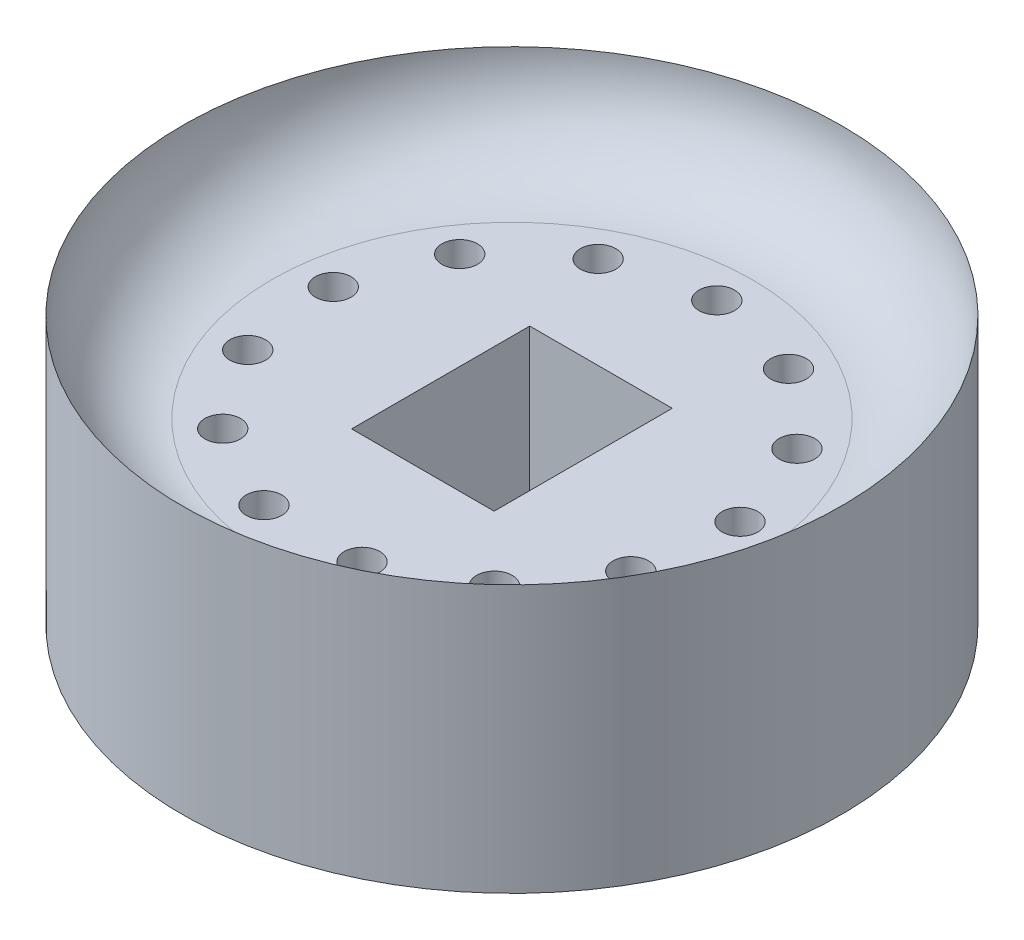
SolidWorks part; units mm, degrees
ref_plane "Alzado" through (0, 0, 0) normal (0, 0, 1) x (1, 0, 0)
ref_plane "Planta" through (0, 0, 0) normal (0, 1, 0) x (1, 0, 0)
ref_plane "Vista lateral" through (0, 0, 0) normal (1, 0, 0) x (0, 0, -1)
sketch "Croquis1" plane through (0, 0, 0) normal (0, 0, 1) x (1, 0, 0)
  line L0 (6.75, 5) -> (0, 5)
  line L1 (0, 0) -> (9.25, 0)
  line L2 (0, 0) -> (0, 7.5)
  line L3 (0, 7.5) -> (9.25, 7.5)
  line L4 (9.25, 0) -> (9.25, 7.5)
  circle A0 centre (6.75, 7.5) radius 2.5
  dimension "D1" = 9.25
  dimension "D2" = 7.5
  dimension "D3" = 2.5
revolve "Revolución1" add sketch "Croquis1" angle 360 about L2
sketch "Croquis2" plane through (0, 5, 0) normal (0, 1, 0) x (1, 0, 0)
  line L1 (-2, -2.5) -> (2, -2.5)
  line L2 (-2, -2.5) -> (-2, 2.5)
  line L3 (-2, 2.5) -> (2, 2.5)
  line L4 (2, -2.5) -> (2, 2.5)
  line L5 (-2, -2.5) -> (2, 2.5) construction
  line L6 (-2, 2.5) -> (2, -2.5) construction
  circle A0 centre (0, 5.75) radius 0.5
  circle A1 centre (2.6722, 5.0914) radius 0.5
  circle A2 centre (4.7322, 3.2664) radius 0.5
  circle A3 centre (5.7081, 0.6931) radius 0.5
  circle A4 centre (5.3763, -2.039) radius 0.5
  circle A5 centre (3.813, -4.3039) radius 0.5
  circle A6 centre (1.3761, -5.5829) radius 0.5
  circle A7 centre (-1.3761, -5.5829) radius 0.5
  circle A8 centre (-3.813, -4.3039) radius 0.5
  circle A9 centre (-5.3763, -2.039) radius 0.5
  circle A10 centre (-5.7081, 0.6931) radius 0.5
  circle A11 centre (-4.7322, 3.2664) radius 0.5
  circle A12 centre (-2.6722, 5.0914) radius 0.5
  point P2 (0, 0)
  point P29 (0, 0)
  dimension "D1" = 1
  dimension "D3" = 4
  dimension "D4" = 5
  dimension "D5" = 5.75
  dimension "D2" = 13
extrude "Cortar-Extruir1" cut sketch "Croquis2" against normal through all
